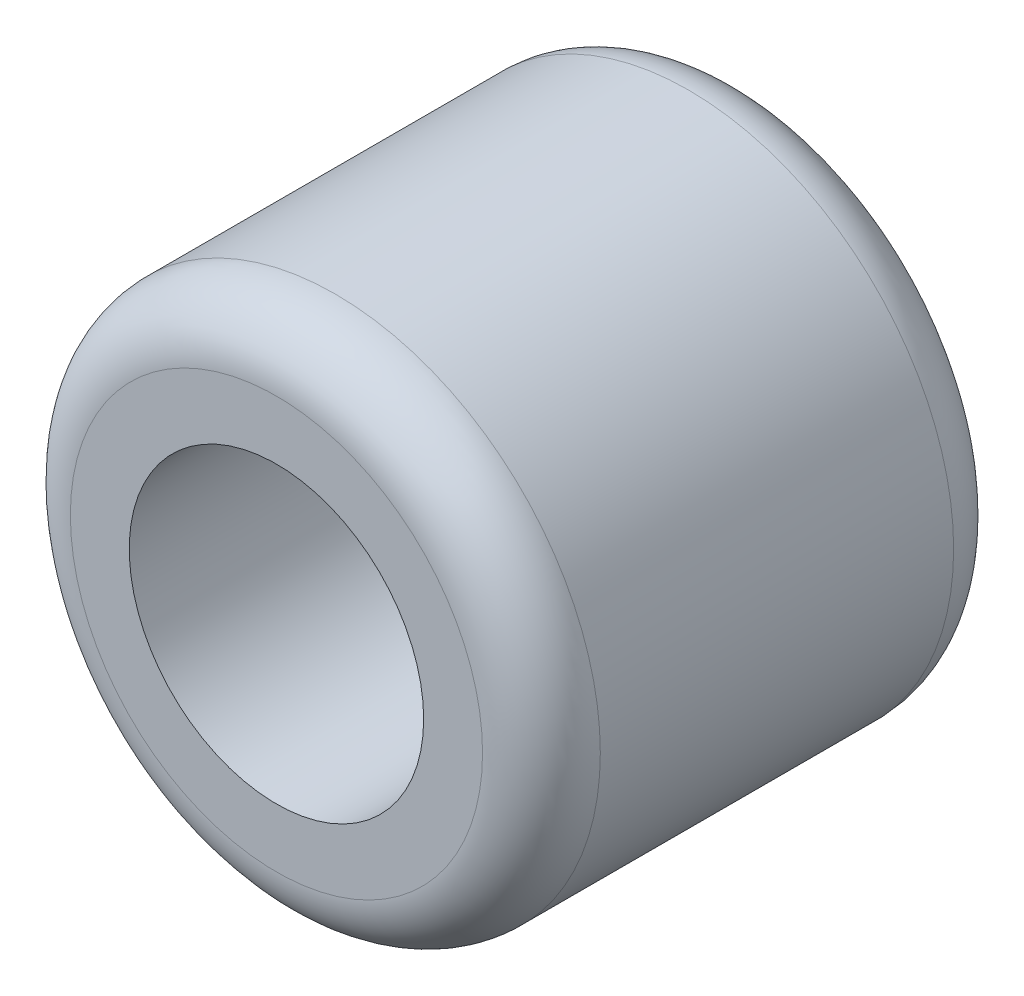
SolidWorks part; units mm, degrees
ref_plane "Front plane" through (0, 0, 0) normal (0, 0, 1) x (1, 0, 0)
ref_plane "Top plane" through (0, 0, 0) normal (0, 1, 0) x (1, 0, 0)
ref_plane "Right Plane" through (0, 0, 0) normal (1, 0, 0) x (0, 0, -1)
sketch "Sketch1" plane through (0, 0, 0) normal (0, 0, 1) x (1, 0, 0)
  circle A0 centre (0, 0) radius 2.5
  circle A1 centre (0, 0) radius 4.5
  dimension "D1" = 5
  dimension "D2" = 9
extrude "Boss-Extrude1" add sketch "Sketch1" along normal blind 8
fillet "Fillet1" radius 1 2 edges at (4.5, 0, 0) (4.5, 0, 8)
